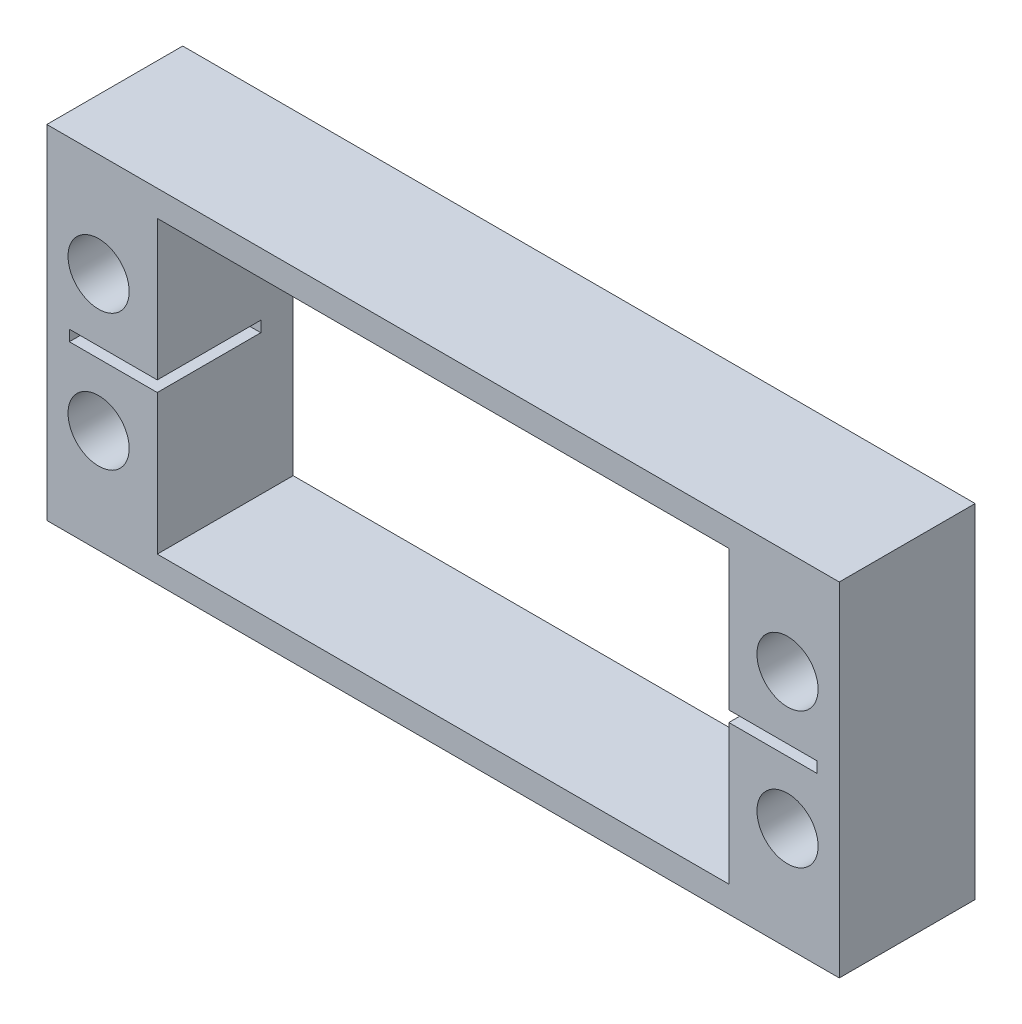
SolidWorks part; units mm, degrees
ref_plane "Front Plane" through (0, 0, 0) normal (0, 0, 1) x (1, 0, 0)
ref_plane "Top Plane" through (0, 0, 0) normal (0, 1, 0) x (1, 0, 0)
ref_plane "Right Plane" through (0, 0, 0) normal (1, 0, 0) x (0, 0, -1)
sketch "Sketch1" plane through (0, 0, 0) normal (0, 0, 1) x (1, 0, 0)
  circle A0 centre (25.072, 28.9393) radius 2.25
  circle A1 centre (25.072, 38.9393) radius 2.25
  circle A2 centre (75.772, 38.9393) radius 2.25
  circle A3 centre (75.772, 28.9393) radius 2.25
sketch "Sketch2" plane through (0, 0, 0) normal (0, 0, 1) x (1, 0, 0)
  line L1 (21.262, 46.5593) -> (79.582, 46.5593)
  line L2 (21.262, 46.5593) -> (21.262, 21.3193)
  line L3 (21.262, 21.3193) -> (79.582, 21.3193)
  line L4 (79.582, 46.5593) -> (79.582, 21.3193)
  dimension "D1" = 7.62
  dimension "D2" = 7.62
  dimension "D3" = 3.81
  dimension "D4" = 3.81
extrude "Boss-Extrude1" add sketch "Sketch2" along normal mid plane 10
extrude "Cut-Extrude1" cut sketch "Sketch1" along normal through all both and the other way through all
sketch "Sketch3" plane through (0, 0, 5) normal (0, 0, 1) x (1, 0, 0)
  line L1 (29.39, 44.6393) -> (71.454, 44.6393)
  line L2 (29.39, 44.6393) -> (29.39, 23.2393)
  line L3 (29.39, 23.2393) -> (71.454, 23.2393)
  line L4 (71.454, 44.6393) -> (71.454, 23.2393)
  circle A2 centre (25.072, 28.9393) radius 2.25 construction
  circle A3 centre (25.072, 38.9393) radius 2.25 construction
  circle A4 centre (75.772, 38.9393) radius 2.25 construction
  dimension "D1" = 5.7
  dimension "D2" = 5.7
  dimension "D3" = 4.318
  dimension "D4" = 4.318
extrude "Cut-Extrude2" cut sketch "Sketch3" against normal through all both and the other way through all
sketch "Sketch4" plane through (0, 0, 5) normal (0, 0, -1) x (-1, 0, 0)
  line L0 (-79.582, 33.9393) -> (-21.262, 33.9393) construction
  line L1 (-79.582, 21.3193) -> (-79.582, 46.5593) construction
  line L2 (-21.262, 46.5593) -> (-21.262, 21.3193) construction
  line L3 (-71.454, 23.2393) -> (-71.454, 44.6393) construction
  line L4 (-77.924, 33.5393) -> (-71.454, 33.5393)
  line L5 (-77.924, 33.5393) -> (-77.924, 34.3393)
  line L6 (-77.924, 34.3393) -> (-71.454, 34.3393)
  line L7 (-71.454, 33.5393) -> (-71.454, 34.3393)
  line L8 (-77.924, 33.5393) -> (-71.454, 34.3393) construction
  line L9 (-77.924, 34.3393) -> (-71.454, 33.5393) construction
  line L10 (-29.39, 44.6393) -> (-29.39, 23.2393) construction
  line L11 (-22.92, 33.5393) -> (-29.39, 33.5393)
  line L12 (-22.92, 33.5393) -> (-22.92, 34.3393)
  line L13 (-22.92, 34.3393) -> (-29.39, 34.3393)
  line L14 (-29.39, 33.5393) -> (-29.39, 34.3393)
  line L15 (-22.92, 33.5393) -> (-29.39, 34.3393) construction
  line L16 (-22.92, 34.3393) -> (-29.39, 33.5393) construction
  point P6 (-74.689, 33.9393)
  point P13 (-26.155, 33.9393)
  dimension "D1" = 6.47
  dimension "D2" = 6.47
  dimension "D3" = 0.8
  dimension "D4" = 0.8
extrude "Cut-Extrude3" cut sketch "Sketch4" along normal blind 7.62
